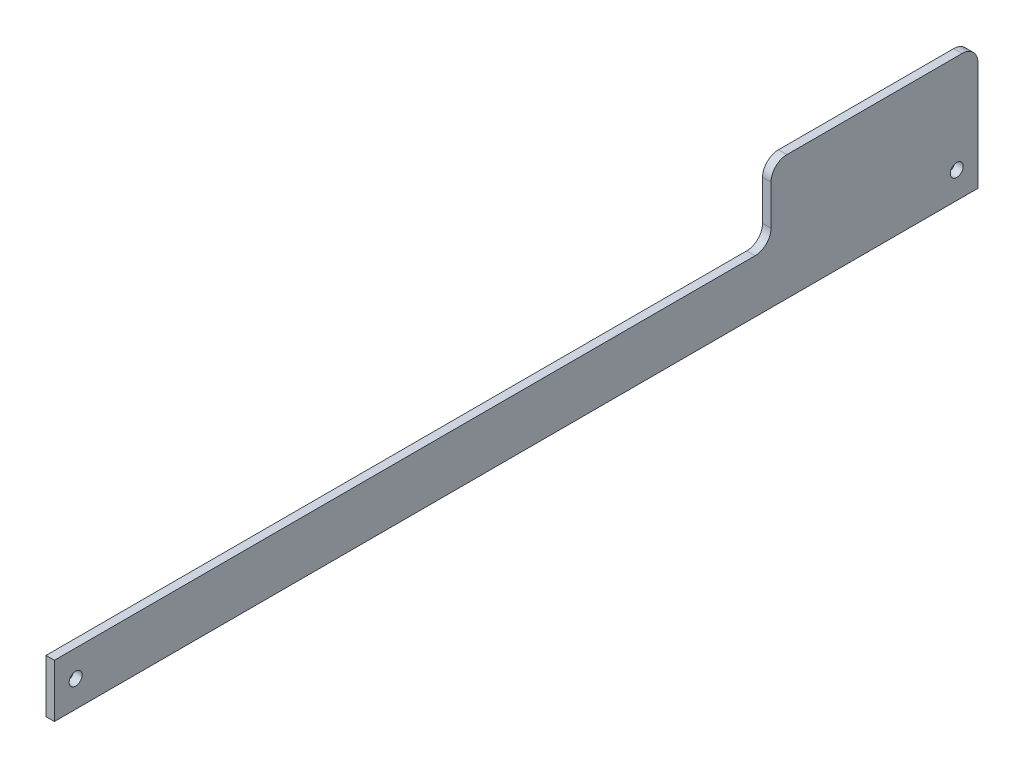
SolidWorks part; units mm, degrees
material "cirlex"
ref_plane "Front" through (0, 0, 0) normal (0, 0, 1) x (1, 0, 0)
ref_plane "Top" through (0, 0, 0) normal (0, 1, 0) x (1, 0, 0)
ref_plane "Right" through (0, 0, 0) normal (1, 0, 0) x (0, 0, -1)
sketch "Sketch1" plane through (0, 0, 0) normal (1, 0, 0) x (0, 0, -1)
  line L0 (0, 0) -> (174, 0)
  line L1 (174, 0) -> (174, 23.5)
  line L2 (174, 23.5) -> (135, 23.5)
  line L3 (135, 23.5) -> (135, 10)
  line L4 (135, 10) -> (0, 10)
  line L5 (0, 10) -> (0, 0)
  dimension "D2" = 39
  dimension "D3" = 23.5
  dimension "D4" = 10
  dimension "D5" = 174
extrude "Boss-Extrude1" add sketch "Sketch1" along normal blind 1.5875
hole_wizard "#2 Clearance Hole1" positions "Sketch3" profile "Sketch2" hole size "#2" standard "ANSI Inch" end condition through all
sketch "Sketch3" plane through (1.5875, 0, 0) normal (1, 0, 0) x (0, 0, -1)
  line L0 (0, 5) -> (-6.9731, 5) construction
  line L1 (0, 10) -> (0, 0) construction
  line L3 (4, 5) -> (18.8537, 5) construction
  point P0 (4, 5)
  point P16 (170, 5)
  point P23 (0, 5)
  dimension "D2" = 4
  dimension "D3" = 166
sketch "Sketch2" plane through (1.5875, 5, -4) normal (0, 1, 0) x (0, 0, -1)
  line L0 (0, 0) -> (0, 1.5875)
  line L1 (0, 1.5875) -> (1.2192, 1.5875)
  line L2 (1.2192, 1.5875) -> (1.2192, 0)
  line L5 (1.2192, 0) -> (0, 0)
  line L11 (0, -6.35) -> (0, 107.95) construction
  dimension "Thru Hole Dia." = 2.4384
  dimension "Thru Hole Depth" = 1.5875
fillet "Fillet1" radius 3 3 edges at (0.7937, 10, -135) (0.7937, 23.5, -135) (0.7937, 23.5, -174)
